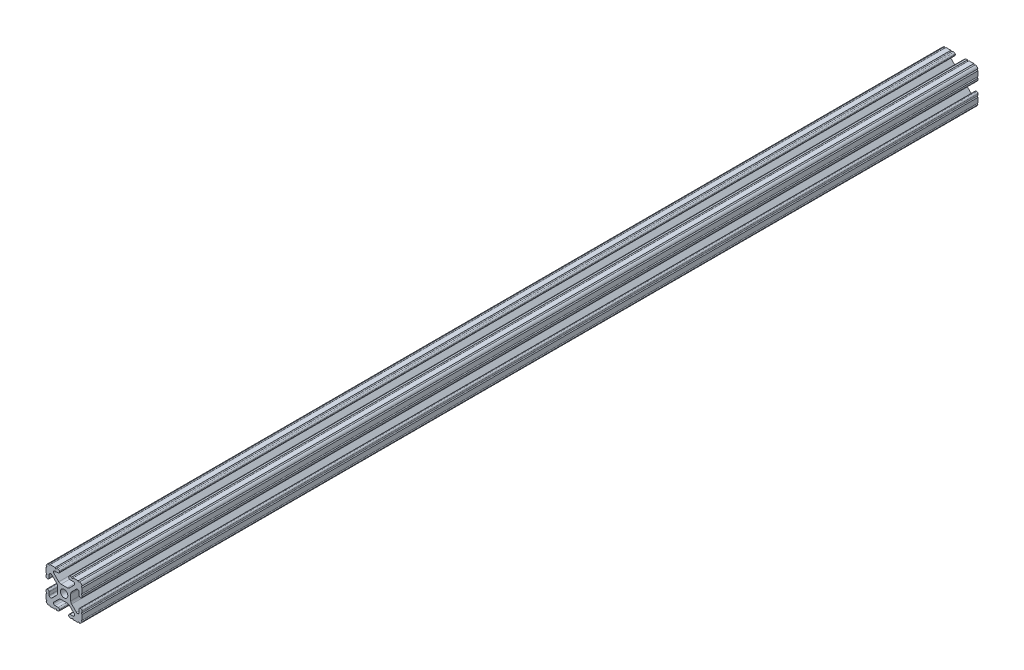
SolidWorks part; units mm, degrees
ref_plane "Front Plane" through (0, 0, 0) normal (0, 0, 1) x (1, 0, 0)
ref_plane "Top Plane" through (0, 0, 0) normal (0, 1, 0) x (1, 0, 0)
ref_plane "Right Plane" through (0, 0, 0) normal (1, 0, 0) x (0, 0, -1)
sketch "Sketch2" plane through (0, 0, 0) normal (0, 0, 1) x (1, 0, 0)
  line L0 (0, 12.7) -> (0, -12.7) construction
  line L1 (-12.7, 0) -> (12.7, 0) construction
  line L2 (3.2512, -12.7) -> (12.7, -12.7)
  line L3 (12.7, -12.7) -> (12.7, -3.2512)
  line L4 (3.2512, -12.7) -> (3.2512, -10.4902)
  line L5 (3.2512, -10.4902) -> (8.9276, -10.4902)
  line L6 (8.9276, -10.4902) -> (3.0856, -4.6482)
  line L7 (0, 0) -> (12.7, -12.7) construction
  line L8 (12.7, -3.2512) -> (10.4902, -3.2512)
  line L9 (10.4902, -3.2512) -> (10.4902, -8.9276)
  line L10 (10.4902, -8.9276) -> (4.6482, -3.0856)
  circle A0 centre (0, 0) radius 2.6035
  arc A1 (6.3485, -10.4902) -> (7.1039, -8.6665) centre (6.3485, -9.4219) ccw construction
  point P8 (0, -4.6482)
  dimension "Center Hole Diameter" = 5.207
  dimension "Rail Height" = 25.4
  dimension "Rail Width" = 25.4
  dimension "T-Slot Width" = 6.5024
  dimension "Slot Inner Width" = 14.8336
  dimension "Thickness" = 2.2098
  dimension "Slot Depth" = 5.842
  dimension "D1" = 2.2098
sketch "Sketch3" plane through (0, 0, 0) normal (1, 0, 0) x (0, 0, -1)
  line L0 (-457.2, -12.7) -> (457.2, -12.7) construction
  line L1 (-431.8, 0) -> (431.8, 0) construction
  dimension "Length" = 914.4
  dimension "D1" = 25.4
sketch "Sketch4" plane through (0, 0, 0) normal (0, 0, 1) x (1, 0, 0)
  line L0 (4.1904, -12.7) -> (10.1173, -12.7)
  line L1 (3.2512, -12.7) -> (12.7, -12.7) construction
  line L2 (3.2512, -12.7) -> (3.2512, -10.4902) construction
  line L3 (3.2512, -10.4902) -> (8.9276, -10.4902) construction
  line L4 (3.2512, -11.4294) -> (3.2512, -11.7608)
  line L5 (4.1904, -10.4902) -> (6.3485, -10.4902)
  line L6 (0, -4.6482) -> (2.164, -4.6482)
  line L7 (8.9276, -10.4902) -> (3.0856, -4.6482) construction
  line L8 (3.7373, -5.2999) -> (7.1039, -8.6665)
  line L9 (12.7, -12.7) -> (12.7, -3.2512) construction
  line L10 (10.4902, -8.9276) -> (4.6482, -3.0856) construction
  line L11 (10.4902, -3.2512) -> (10.4902, -8.9276) construction
  line L12 (10.4902, -6.3485) -> (10.4902, -4.1904)
  line L13 (12.7, -3.2512) -> (10.4902, -3.2512) construction
  line L14 (11.4294, -3.2512) -> (11.7608, -3.2512)
  line L15 (12.7, -4.1904) -> (12.7, -10.1173)
  line L16 (8.6665, -7.1039) -> (5.2999, -3.7373)
  line L17 (4.6482, 0) -> (4.6482, -2.164)
  line L18 (-12.7, 0) -> (12.7, 0) construction
  line L19 (0, -4.6482) -> (0, -2.6035)
  line L20 (0, 12.7) -> (0, -12.7) construction
  line L21 (4.6482, 0) -> (2.6035, 0)
  arc A0 (3.2512, -11.7608) -> (4.1904, -12.7) centre (4.1904, -11.7608) ccw
  arc A2 (3.2512, -11.4294) -> (4.1904, -10.4902) centre (4.1904, -11.4294) cw
  arc A3 (6.3485, -10.4902) -> (7.1039, -8.6665) centre (6.3485, -9.4219) ccw
  arc A4 (2.164, -4.6482) -> (3.7373, -5.2999) centre (2.164, -6.8732) cw
  arc A5 (10.1173, -12.7) -> (12.7, -10.1173) centre (10.1173, -10.1173) ccw
  arc A6 (8.6665, -7.1039) -> (10.4902, -6.3485) centre (9.4219, -6.3485) ccw
  arc A7 (10.4902, -4.1904) -> (11.4294, -3.2512) centre (11.4294, -4.1904) cw
  arc A8 (11.7608, -3.2512) -> (12.7, -4.1904) centre (11.7608, -4.1904) cw
  arc A9 (5.2999, -3.7373) -> (4.6482, -2.164) centre (6.8732, -2.164) cw
  circle A10 centre (0, 0) radius 2.6035 construction
  arc A11 (0, -2.6035) -> (2.6035, 0) centre (0, 0) ccw
  dimension "D1" = 2.5827
  dimension "D2" = 2.225
  dimension "D3" = 0.9392
extrude "Boss-Extrude1" add sketch "Sketch4" along normal mid plane 914.4
sketch "Sketch5" plane through (0, 0, 0) normal (0, 0, 1) x (1, 0, 0)
  line L0 (3.2512, -12.7) -> (12.7, -12.7) construction
  line L1 (4.1904, -10.4902) -> (6.3485, -10.4902) construction
  line L3 (0, 0) -> (12.7, -12.7) construction
  line L4 (6.3485, -10.4902) -> (6.3485, -12.7) construction
  line L5 (8.9276, -10.4902) -> (3.0856, -4.6482) construction
  circle A0 centre (10.3562, -12.7) radius 0.5524
  circle A1 centre (5.796, -12.7) radius 0.5524
  circle A2 centre (12.7, -10.3562) radius 0.5524
  circle A3 centre (12.7, -5.796) radius 0.5524
  point P10 (5.2694, -10.4902)
  point P12 (9.4219, -6.3485)
  dimension "D1" = 1.1049
extrude "Cut-Extrude1" cut sketch "Sketch5" against normal through all both and the other way through all
mirror "Mirror1" about plane through (0, 0, 0) normal (1, 0, 0) of bodies 137 134
mirror "Mirror2" about plane through (0, 0, 0) normal (0, 1, 0) of bodies 135
sketch "Sketch6" plane through (0, 0, 0) normal (1, 0, 0) x (0, 0, -1)
  line L0 (457.2, 9.8037) -> (457.2, 6.3485) construction
  line L1 (-623.861, 69.6325) -> (-171.25, 69.6325)
  line L2 (-623.861, 69.6325) -> (-623.861, -86.5432)
  line L3 (-623.861, -86.5432) -> (-171.25, -86.5432)
  line L4 (-171.25, 69.6325) -> (-171.25, -86.5432)
  dimension "D1" = 628.45
extrude "Cut-Extrude2" cut sketch "Sketch6" against normal mid plane 27.94
equation "\"D1@Boss-Extrude1\"=\"Length@Sketch3\""
equation "\"D1@Sketch2\"=\"Thickness@Sketch2\""
equation "\"D2@Sketch4\"=\"Slot Inner Width@Sketch2\"*0.15"
equation "\"D1@Sketch4\"=\"D3@Sketch4\"*2.75"
equation "\"D3@Sketch4\"=\"Thickness@Sketch2\"*0.425"
equation "\"D1@Sketch5\"=\"Thickness@Sketch2\"*0.5"
